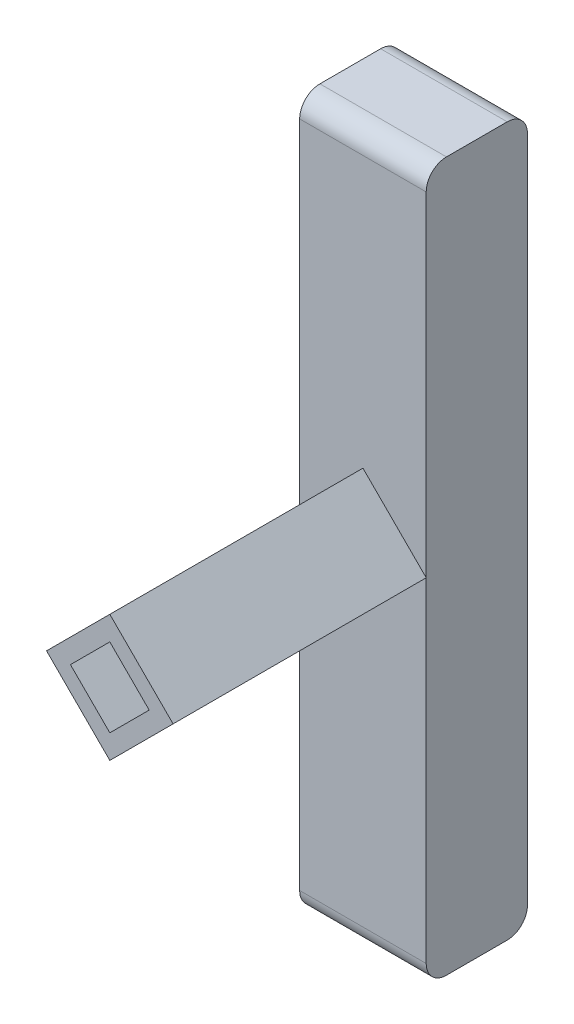
SolidWorks part; units mm, degrees
ref_plane "Plan de face" through (0, 0, 0) normal (0, 0, 1) x (1, 0, 0)
ref_plane "Plan de dessus" through (0, 0, 0) normal (0, 1, 0) x (1, 0, 0)
ref_plane "Plan de droite" through (0, 0, 0) normal (1, 0, 0) x (0, 0, -1)
sketch "Esquisse1" plane through (0, 0, 0) normal (0, 0, 1) x (1, 0, 0)
  line L1 (-6.25, 35) -> (6.25, 35)
  line L2 (-6.25, 35) -> (-6.25, -35)
  line L3 (-6.25, -35) -> (6.25, -35)
  line L4 (6.25, 35) -> (6.25, -35)
  line L5 (-6.25, 35) -> (6.25, -35) construction
  line L6 (-6.25, -35) -> (6.25, 35) construction
  point P0 (0, 0)
  dimension "D1" = 70
  dimension "D2" = 12.5
extrude "Boss.-Extru.1" add sketch "Esquisse1" along normal blind 10
sketch "Esquisse2" plane through (0, 0, 0) normal (0, 0, -1) x (-1, 0, 0)
  line L0 (6.25, 0) -> (0, 6.25)
  line L5 (0, 6.25) -> (0, -6.25) construction
  line L6 (-6.25, 0) -> (6.25, 0) construction
  line L7 (6.25, 0) -> (0, -6.25)
  line L8 (0, 6.25) -> (-6.25, 0)
  line L9 (0, -6.25) -> (-6.25, 0)
  point P0 (0, 0)
  dimension "D2" = 12.5
extrude "Boss.-Extru.2" add sketch "Esquisse2" against normal blind 35
sketch "Esquisse3" plane through (0, 0, 0) normal (0, 0, -1) x (-1, 0, 0)
  line L1 (-3.8891, 0) -> (0, 3.8891)
  line L2 (-3.8891, 0) -> (0, -3.8891)
  line L3 (0, -3.8891) -> (3.8891, 0)
  line L4 (0, 3.8891) -> (3.8891, 0)
  line L5 (-3.8891, 0) -> (3.8891, 0) construction
  line L6 (0, -3.8891) -> (0, 3.8891) construction
  point P0 (0, 0)
  point P6 (0, 0)
  dimension "D1" = 5.5
extrude "Enlèv. mat.-Extru.1" cut sketch "Esquisse3" against normal blind 40
fillet "Congé3" radius 2 4 edges at (0, -35, 10) (0, -35, 0) (0, 35, 0) (0, 35, 10)
